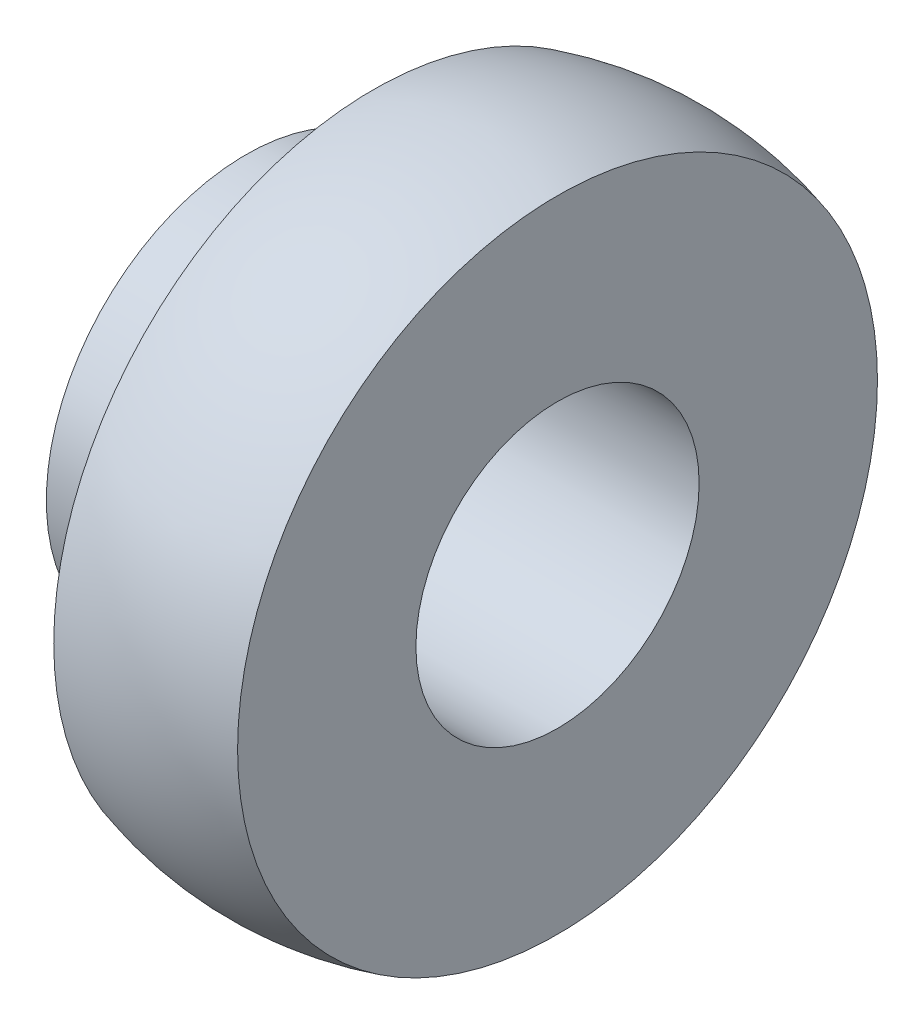
SolidWorks part; units mm, degrees
ref_plane "Płaszczyzna XY" through (0, 0, 0) normal (0, 0, 1) x (1, 0, 0)
ref_plane "Płaszczyzna XZ" through (0, 0, 0) normal (0, 1, 0) x (1, 0, 0)
ref_plane "Płaszczyzna YZ" through (0, 0, 0) normal (1, 0, 0) x (0, 0, -1)
sketch "Szkic1" plane through (0, 0, 0) normal (0, 1, 0) x (1, 0, 0)
  line L1 (6.4701, -10) -> (-15.5293, -10)
  line L6 (6.4701, -22.5918) -> (6.4701, -10)
  line L7 (-15.5293, -10) -> (-15.5293, -14.1)
  line L8 (-15.5293, -14.1) -> (-10.0293, -14.1)
  line L9 (6.4701, -10) -> (6.4701, 0)
  line L10 (6.4701, 0) -> (-15.5293, 0)
  line L11 (-15.5293, 0) -> (-15.5293, -10)
  line L12 (6.4676, -22.5925) -> (6.4676, -10)
  line L13 (-6.5324, -22.5738) -> (-6.5324, -14.1)
  line L14 (-6.5324, -14.1) -> (-10.0293, -14.1)
  arc A1 (-6.5324, -22.5738) -> (6.4701, -22.5918) centre (0, 0) ccw
  point P6 (-0.0324, -23.5)
  point P8 (6.4676, -22.5925)
  point P12 (-6.5324, -22.5738)
  dimension "D1" = 23.5
  dimension "D3" = 6.5
  dimension "D4" = 6.5
revolve "Obrót2" add sketch "Szkic1" angle 360 about L10
sketch "Szkic2" plane through (0, 0, 0) normal (0, 1, 0) x (1, 0, 0)
  arc A0 (6.4676, 22.5925) -> (-6.5324, 22.5738) centre (0, 0) ccw construction
  arc A1 (6.4676, 22.5925) -> (-6.5324, 22.5738) centre (0, 0) ccw
